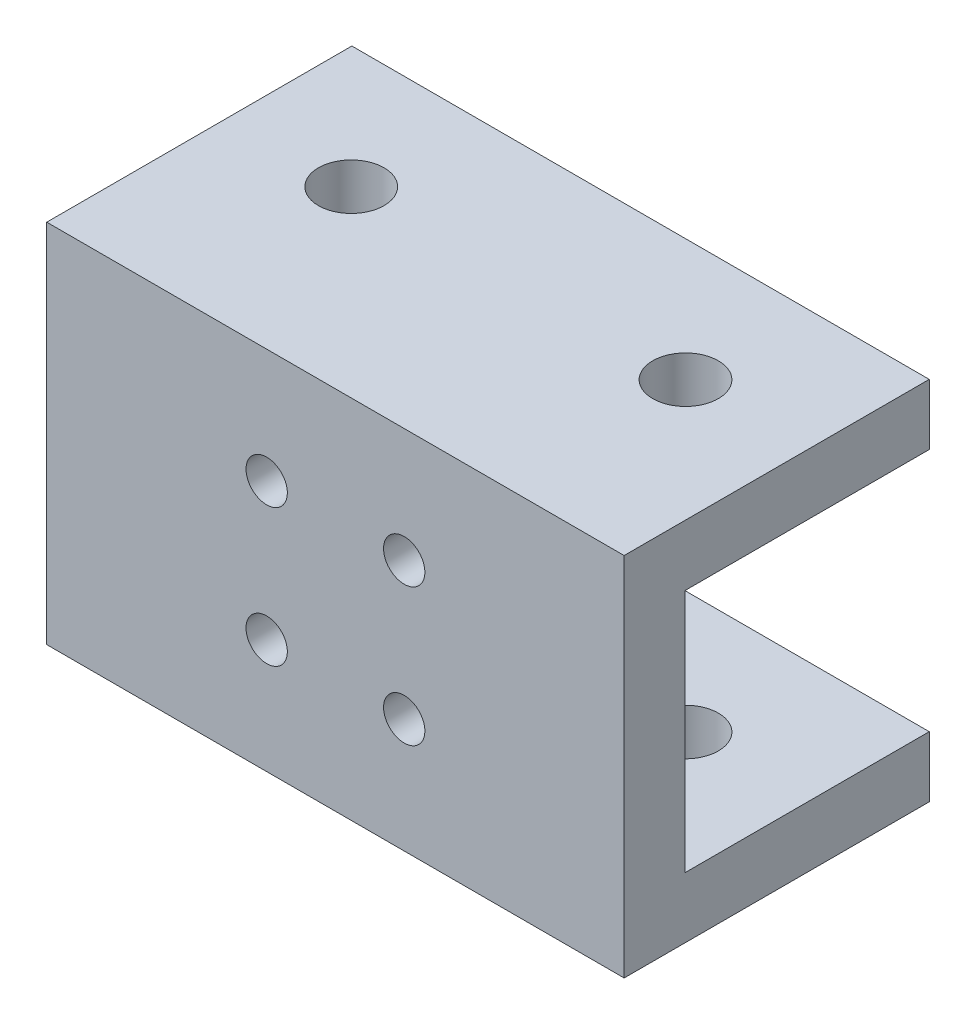
SolidWorks part; units mm, degrees
ref_plane "Front Plane" through (0, 0, 0) normal (0, 0, 1) x (1, 0, 0)
ref_plane "Top Plane" through (0, 0, 0) normal (0, 1, 0) x (1, 0, 0)
ref_plane "Right Plane" through (0, 0, 0) normal (1, 0, 0) x (0, 0, -1)
sketch "Sketch1" plane through (0, 0, 0) normal (1, 0, 0) x (0, 0, -1)
  line L0 (10.05, -10.05) -> (10.05, -15.05)
  line L1 (10.05, -10.05) -> (-10.05, -10.05) construction
  line L2 (10.05, -10.05) -> (10.05, 10.05) construction
  line L3 (10.05, 10.05) -> (-10.05, 10.05) construction
  line L4 (-10.05, -10.05) -> (-10.05, 10.05) construction
  line L5 (10.05, -10.05) -> (-10.05, 10.05) construction
  line L6 (10.05, 10.05) -> (-10.05, -10.05) construction
  line L7 (10.05, -15.05) -> (-15.05, -15.05) construction
  line L8 (10.05, -15.05) -> (10.05, 15.05) construction
  line L9 (10.05, 15.05) -> (-15.05, 15.05) construction
  line L10 (-15.05, -15.05) -> (-15.05, 15.05) construction
  line L11 (10.05, -15.05) -> (-15.05, 15.05) construction
  line L12 (10.05, 15.05) -> (-15.05, -15.05) construction
  line L13 (10.05, -15.05) -> (-15.05, -15.05)
  line L14 (-15.05, -15.05) -> (-15.05, 15.05)
  line L15 (-15.05, 15.05) -> (10.05, 15.05)
  line L16 (10.05, 15.05) -> (10.05, 10.05)
  line L17 (10.05, 10.05) -> (-10.05, 10.05)
  line L18 (-10.05, 10.05) -> (-10.05, -10.05)
  line L19 (-10.05, -10.05) -> (10.05, -10.05)
  line L20 (-10.05, 10.05) -> (-15.05, 10.05) construction
  point P0 (0, 0)
  point P6 (-2.5, 0)
  dimension "D1" = 20.1
  dimension "D2" = 5
extrude "Boss-Extrude1" add sketch "Sketch1" along normal blind 47.5
sketch "Sketch2" plane through (0, 0, 10.05) normal (0, 0, -1) x (-1, 0, 0)
  line L1 (-23.75, 0) -> (-23.75, 10.05) construction
  line L2 (-47.5, 10.05) -> (0, 10.05) construction
  line L3 (-29.4069, 5.6569) -> (-23.75, 0) construction
  line L4 (0, 0) -> (-47.5, 0) construction
  line L5 (0, -10.05) -> (0, 10.05) construction
  line L6 (-47.5, -10.05) -> (-47.5, 10.05) construction
  circle A0 centre (-23.75, 0) radius 11.5 construction
  circle A1 centre (-29.4069, 5.6569) radius 1.5
  circle A2 centre (-18.0931, 5.6569) radius 1.5
  circle A3 centre (-18.0931, -5.6569) radius 1.5
  circle A4 centre (-29.4069, -5.6569) radius 1.5
  point P2 (0, 0)
  point P16 (-23.75, 0)
  dimension "D1" = 23
  dimension "D2" = 3
  dimension "D3" = 8
  dimension "D5" = 45
  dimension "D4" = 4
hole_wizard "CSK for M3 Flat Head Machine Screw1" positions "Sketch3" profile "Sketch4" countersink size "M3" standard "ANSI Metric" end condition through all
sketch "Sketch3" plane through (0, 0, 10.05) normal (0, 0, -1) x (-1, 0, 0)
  point P0 (-29.4069, 5.6569)
  point P3 (-18.0931, 5.6569)
  point P6 (-18.0931, -5.6569)
  point P9 (-29.4069, -5.6569)
sketch "Sketch4" plane through (29.4069, 5.6569, 10.05) normal (1, 0, 0) x (0, 1, 0)
  line L0 (0, 0) -> (0, 5)
  line L1 (0, 5) -> (1.7, 5)
  line L2 (1.7, 5) -> (1.7, 1.45)
  line L3 (1.7, 1.45) -> (3.15, 0)
  line L5 (3.15, 0) -> (0, 0)
  line L6 (-1.7, 1.45) -> (-3.15, 0) construction
  line L11 (0, -6.35) -> (0, 107.95) construction
  dimension "Thru Hole Dia." = 3.4
  dimension "Thru Hole Depth" = 5
  dimension "Near C'Sink Dia." = 6.3
  dimension "Near C'Sink Angle" = 90
sketch "Sketch5" plane through (0, 15.05, 0) normal (0, 1, 0) x (1, 0, 0)
  line L0 (0, 0) -> (47.5, 0) construction
  line L1 (47.5, 10.05) -> (47.5, -15.05) construction
  line L2 (0, 10.05) -> (0, -15.05) construction
  circle A0 centre (10, 0) radius 2.7
  circle A1 centre (37.5, 0) radius 2.7
  dimension "D1" = 5.4
  dimension "D2" = 10
  dimension "D3" = 10
extrude "Cut-Extrude1" cut sketch "Sketch5" against normal through all
